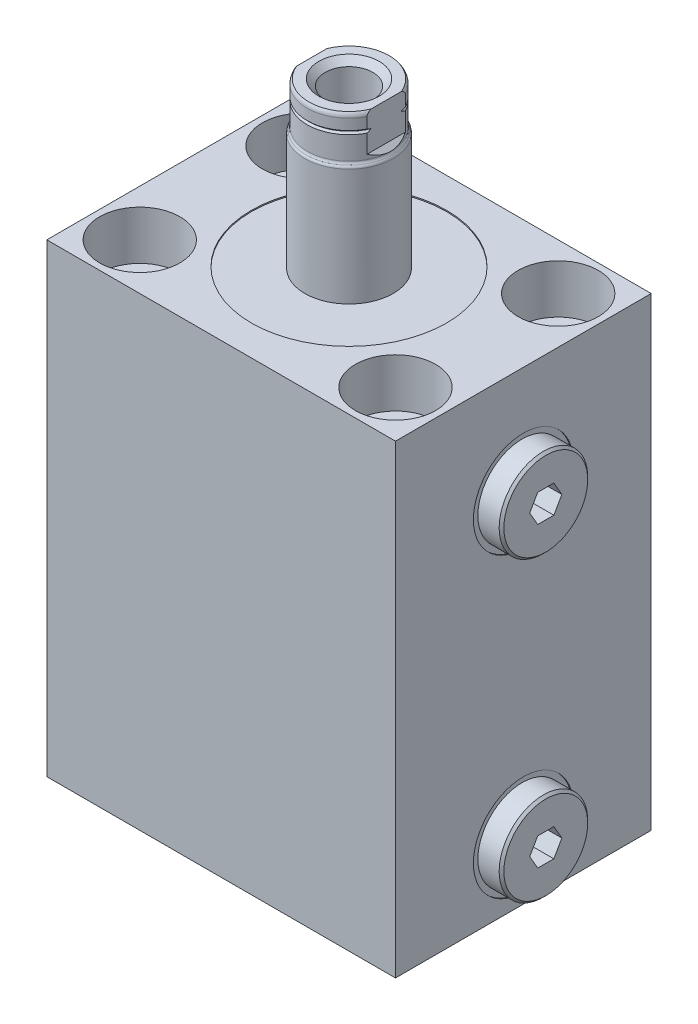
SolidWorks part; units mm, degrees
material "Alloy Steel"
ref_plane "Front Plane" through (0, 0, 0) normal (0, 0, 1) x (1, 0, 0)
ref_plane "Top Plane" through (0, 0, 0) normal (0, 1, 0) x (1, 0, 0)
ref_plane "Right Plane" through (0, 0, 0) normal (1, 0, 0) x (0, 0, -1)
sketch "Sketch1" plane through (0, 0, 0) normal (0, 1, 0) x (1, 0, 0)
  line L0 (-37.5, 27.5) -> (37.5, -27.5) construction
  line L1 (-37.5, 27.5) -> (37.5, 27.5)
  line L2 (-37.5, 27.5) -> (-37.5, -27.5)
  line L3 (-37.5, -27.5) -> (37.5, -27.5)
  line L4 (37.5, 27.5) -> (37.5, -27.5)
  point P4 (0, 0)
  dimension "D1" = 75
  dimension "D2" = 55
extrude "Extrude1" add sketch "Sketch1" along normal blind 100
sketch "Sketch2" plane through (0, 100, 0) normal (0, 1, 0) x (1, 0, 0)
  circle A0 centre (0, 0) radius 21
  dimension "D1" = 42
extrude "Cut-Extrude1" cut sketch "Sketch2" against normal blind 0.254
sketch "Sketch3" plane through (0, 0, 0) normal (0, 0, 1) x (1, 0, 0)
  line L0 (-6.848, 77) -> (35.4055, 77) construction
  line L1 (-37.5, 0) -> (37.5, 0) construction
  line L2 (37.5, 77) -> (37.5, 66.256)
  line L3 (37.5, 100) -> (37.5, 0) construction
  line L4 (37.5, 66.256) -> (37.246, 66.256)
  line L5 (37.246, 66.256) -> (37.246, 70.3452)
  line L6 (37.246, 70.3452) -> (36.5348, 71.0564)
  line L7 (36.5348, 71.0564) -> (21.752, 71.0564)
  line L8 (21.752, 71.0564) -> (21.752, 77)
  line L9 (21.752, 77) -> (37.5, 77)
  dimension "D1" = 77
  dimension "D2" = 21.488
  dimension "D3" = 0.254
  dimension "D4" = 11.8872
  dimension "D5" = 15.748
  dimension "D6" = 45
  dimension "D7" = 0.7112
revolve "Cut-Revolve1" cut sketch "Sketch3" angle 360 about L0
sketch "Sketch4" plane through (0, 0, 0) normal (0, 0, 1) x (1, 0, 0)
  line L0 (25.308, 77) -> (25.308, 82.9182)
  line L1 (36.5348, 77) -> (21.752, 77) construction
  line L2 (25.308, 82.9182) -> (37.246, 82.9182)
  line L3 (37.246, 82.9182) -> (37.246, 86.525)
  line L4 (37.246, 86.525) -> (42.326, 86.525)
  line L5 (42.326, 86.525) -> (42.326, 77)
  line L6 (42.326, 77) -> (25.308, 77)
  line L8 (37.246, 66.256) -> (37.246, 87.744) construction
  line L9 (8.7326, 77) -> (38.9701, 77) construction
  dimension "D1" = 11.938
  dimension "D2" = 11.8364
  dimension "D3" = 5.08
  dimension "D4" = 19.05
revolve "Revolve1" add sketch "Sketch4" angle 360 about L9
chamfer "Chamfer1" distance 0.508 angle 45 1 edges at (42.326, 77, 9.525)
sketch "Sketch5" plane through (42.326, 0, 0) normal (1, 0, 0) x (0, 0, -1)
  line L1 (1.7304, 79.9972) -> (-1.7304, 79.9972)
  line L2 (-1.7304, 79.9972) -> (-3.4609, 77)
  line L3 (-3.4609, 77) -> (-1.7304, 74.0028)
  line L4 (-1.7304, 74.0028) -> (1.7304, 74.0028)
  line L5 (1.7304, 74.0028) -> (3.4609, 77)
  line L6 (3.4609, 77) -> (1.7304, 79.9972)
  circle A0 centre (0, 77) radius 2.9972 construction
  dimension "D1" = 5.9944
extrude "Cut-Extrude2" cut sketch "Sketch5" against normal blind 5.9944
pattern_linear "LPattern1" count 2 spacing 64 along (0, -1, 0) of "Cut-Revolve1", "Revolve1", "Chamfer1", "Cut-Extrude2"
sketch "Sketch6" plane through (0, 0, 0) normal (0, 0, 1) x (1, 0, 0)
  line L0 (-37.5, 0) -> (37.5, 0) construction
  line L1 (0, 0) -> (0, 18.7888) construction
  line L12 (0, 0) -> (0, 14.8958)
  line L13 (5.7025, 0) -> (0, 0)
  line L14 (1.2446, 14.148) -> (0, 14.8958)
  line L15 (1.2446, 4.9529) -> (1.2446, 14.148)
  line L16 (1.7525, 4.445) -> (1.2446, 4.9529)
  line L17 (3.2512, 4.445) -> (1.7525, 4.445)
  line L18 (3.2512, 1.448) -> (3.2512, 4.445)
  line L19 (5.7025, 1.448) -> (3.2512, 1.448)
  line L20 (5.7025, 0) -> (5.7025, 1.448)
  dimension "D1" = 59
  dimension "D2" = 14.8958
  dimension "D3" = 2.4892
  dimension "D4" = 11.405
  dimension "D5" = 1.448
  dimension "D6" = 6.5024
  dimension "D7" = 4.445
  dimension "D8" = 45
  dimension "D9" = 0.5079
revolve "Cut-Revolve2" cut sketch "Sketch6" angle 360 about L1
sketch "Sketch7" plane through (0, 0, 0) normal (0, 0, 1) x (1, 0, 0)
  line L0 (0, 0) -> (0, 17.946) construction
  line L1 (0, 14.148) -> (0, 14.8958) construction
  line L2 (-37.5, 0) -> (37.5, 0) construction
  circle A0 centre (4.814, 0.5844) radius 0.889
  dimension "D1" = 9.628
  dimension "D2" = 1.778
  dimension "D3" = 0.5844
revolve "Revolve3" add sketch "Sketch7" angle 360 about L0
pattern_linear "LPattern2" count 2 spacing 27.5 along (-1, 0, 0) of "Cut-Revolve2", "Revolve3"
sketch "Sketch8" plane through (0, 0, 0) normal (0, 0, 1) x (1, 0, 0)
  line L0 (9.5, 99.746) -> (9.5, 124.8713)
  line L1 (8.6341, 135) -> (0, 135)
  line L2 (0, 135) -> (0, 99.746)
  line L3 (9, 134.0094) -> (9, 126)
  line L4 (9.5, 99.746) -> (0, 99.746)
  line L5 (0, 0) -> (0, 83.6966) construction
  line L6 (21, 99.746) -> (-21, 99.746) construction
  line L7 (-37.5, 0) -> (37.5, 0) construction
  arc A0 (9, 134.0094) -> (8.6341, 135) centre (7.476, 134.0094) ccw
  arc A1 (9, 126) -> (9.25, 125.4356) centre (9.762, 126) ccw
  arc A2 (9.5, 124.8713) -> (9.25, 125.4356) centre (8.738, 124.8713) ccw
  dimension "D1" = 1.524
  dimension "D7" = 0.762
  dimension "D8" = 0.762
  dimension "D2" = 9
  dimension "D3" = 135
  dimension "D4" = 0.9906
  dimension "D5" = 18
  dimension "D6" = 19
revolve "Revolve4" add sketch "Sketch8" angle 360 about L5
sketch "Sketch10" plane through (0, 0, 0) normal (0, 0, 1) x (1, 0, 0)
  line L0 (6.5, 135) -> (5.131, 133.631)
  line L1 (5.131, 133.631) -> (5.131, 114.68)
  line L2 (5.131, 114.68) -> (0, 111.597)
  line L3 (0, 111.597) -> (0, 135)
  line L4 (0, 135) -> (6.5, 135)
  line L5 (0, 135) -> (0, 82.7828) construction
  line L6 (8.6341, 135) -> (-8.6341, 135) construction
  dimension "D1" = 45
  dimension "D2" = 1.369
  dimension "D3" = 10.262
  dimension "D4" = 59
  dimension "D5" = 20.32
revolve "Cut-Revolve3" cut sketch "Sketch10" angle 360 about L5
sketch "Sketch11" plane through (0, 0, 0) normal (0, 0, 1) x (1, 0, 0)
  line L0 (9, 131.698) -> (8.619, 131.317)
  line L1 (8.619, 131.317) -> (9, 130.936)
  line L2 (9, 130.936) -> (9, 131.698)
  line L3 (9, 126) -> (9, 134.0094) construction
  line L4 (8.619, 131.317) -> (9, 131.317) construction
  line L5 (8.6341, 135) -> (-8.6341, 135) construction
  line L6 (0, 0) -> (0, 94.5745) construction
  dimension "D1" = 0.762
  dimension "D2" = 3.683
  dimension "D3" = 90
revolve "Cut-Revolve4" cut sketch "Sketch11" angle 360 about L6
sketch "Sketch12" plane through (0, 0, 0) normal (0, 0, 1) x (1, 0, 0)
  line L0 (0, 0) -> (0, 87.4273) construction
  line L1 (8, 135) -> (8, 127)
  line L2 (6.5, 135) -> (-6.5, 135) construction
  line L3 (8, 127) -> (9.5, 125.5)
  line L4 (9.5, 125.5) -> (9.5, 135)
  line L5 (9.5, 135) -> (8, 135)
  line L6 (9.5, 99.746) -> (9.5, 124.8713) construction
  line L7 (-9.5, 135) -> (-8, 135)
  line L8 (-9.5, 125.5) -> (-9.5, 135)
  line L9 (-8, 127) -> (-9.5, 125.5)
  line L10 (-8, 135) -> (-8, 127)
  dimension "D1" = 16
  dimension "D2" = 45
  dimension "D3" = 8
extrude "Cut-Extrude3" cut sketch "Sketch12" against normal through all and the other way through all
hole_wizard "Hole1" positions "Sketch14" profile "Sketch13" legacy end condition through all
sketch "Sketch14" plane through (0, 100, 0) normal (0, 1, 0) x (-1, 0, 0)
  line L0 (0, 0) -> (0, 30.0241) construction
  line L1 (0, 0) -> (32.2854, 0) construction
  point P0 (27.5, 17.5)
  point P10 (27.5, -17.5)
  point P12 (-27.5, -17.5)
  point P13 (-27.5, 17.5)
  dimension "D1" = 35
  dimension "D2" = 55
sketch "Sketch13" plane through (-27.5, 100, 17.5) normal (1, 0, 0) x (0, 0, 1)
  line L0 (0, 0) -> (0, 100.3046)
  line L1 (0, 100.3046) -> (5.245, 100.3046)
  line L2 (5.245, 100.3046) -> (5.245, 10.49)
  line L3 (5.245, 10.49) -> (8.6235, 10.49)
  line L4 (8.6235, 10.49) -> (8.6235, 0)
  line L5 (8.6235, 0) -> (0, 0)
  line L6 (0, 110) -> (0, -10) construction
  dimension "Diameter" = 10.49
  dimension "Depth" = 100.3046
  dimension "C-Bore Diameter" = 17.247
  dimension "C-Bore Depth" = 10.49
